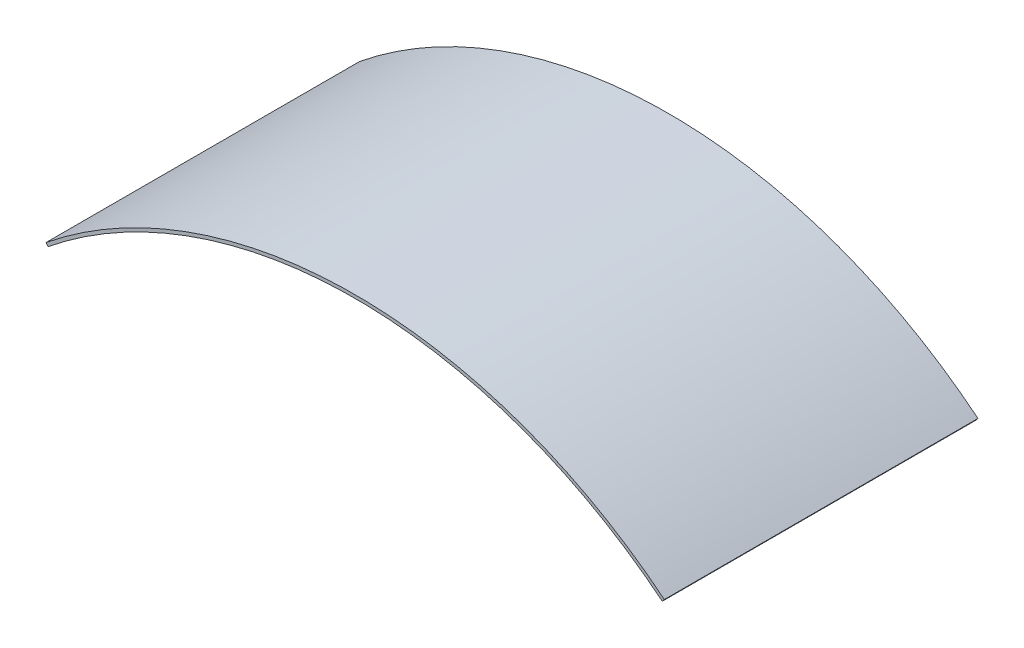
SolidWorks part; units mm, degrees
material "Oak"
ref_plane "Front Plane" through (0, 0, 0) normal (0, 0, 1) x (1, 0, 0)
ref_plane "Top Plane" through (0, 0, 0) normal (0, 1, 0) x (1, 0, 0)
ref_plane "Right Plane" through (0, 0, 0) normal (1, 0, 0) x (0, 0, -1)
sketch "Sketch1" plane through (0, 0, 0) normal (0, 0, 1) x (1, 0, 0)
  line L0 (298.45, 0) -> (-298.45, 0) construction
  line L1 (-298.45, 0) -> (-300.4469, 2.4684)
  line L2 (-298.45, 0) -> (-306.4758, -6.4928) construction
  line L3 (0, 0) -> (0, 105.6068) construction
  line L4 (298.45, 0) -> (300.4469, 2.4684)
  arc A0 (-298.45, 0) -> (298.45, 0) centre (0, -368.9136) cw
  arc A1 (-300.4469, 2.4684) -> (300.4469, 2.4684) centre (0, -368.9136) cw
  arc A2 (299.4485, 1.2342) -> (-299.4485, 1.2342) centre (0, -368.9136) ccw construction
  point P4 (0, 0)
  point P6 (0, 105.6068)
  dimension "D2" = 647.7
  dimension "D1" = 596.9
  dimension "D3" = 3.175
extrude "Boss-Extrude1" add sketch "Sketch1" along normal mid plane 304.8
